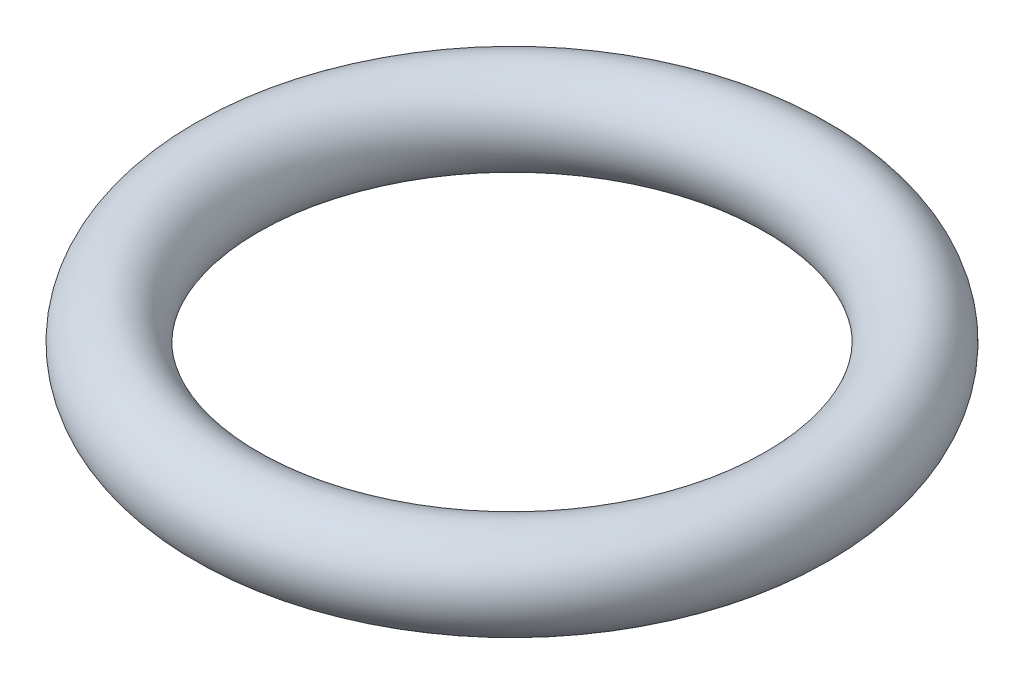
SolidWorks part; units mm, degrees
ref_plane "Front Plane" through (0, 0, 0) normal (0, 0, 1) x (1, 0, 0)
ref_plane "Top Plane" through (0, 0, 0) normal (0, 1, 0) x (1, 0, 0)
ref_plane "Right Plane" through (0, 0, 0) normal (1, 0, 0) x (0, 0, -1)
sketch "Sketch1" plane through (0, 0, 0) normal (0, 0, 1) x (1, 0, 0)
  line L0 (0, -2.4432) -> (0, 2.4432) construction
  line L1 (-8, 0) -> (0, 0) construction
  circle A0 centre (-8, 0) radius 1.25
  point P5 (0, 0)
  dimension "D1" = 2.5
  dimension "D2" = 8
revolve "Revolve1" add sketch "Sketch1" angle 360 about L0
